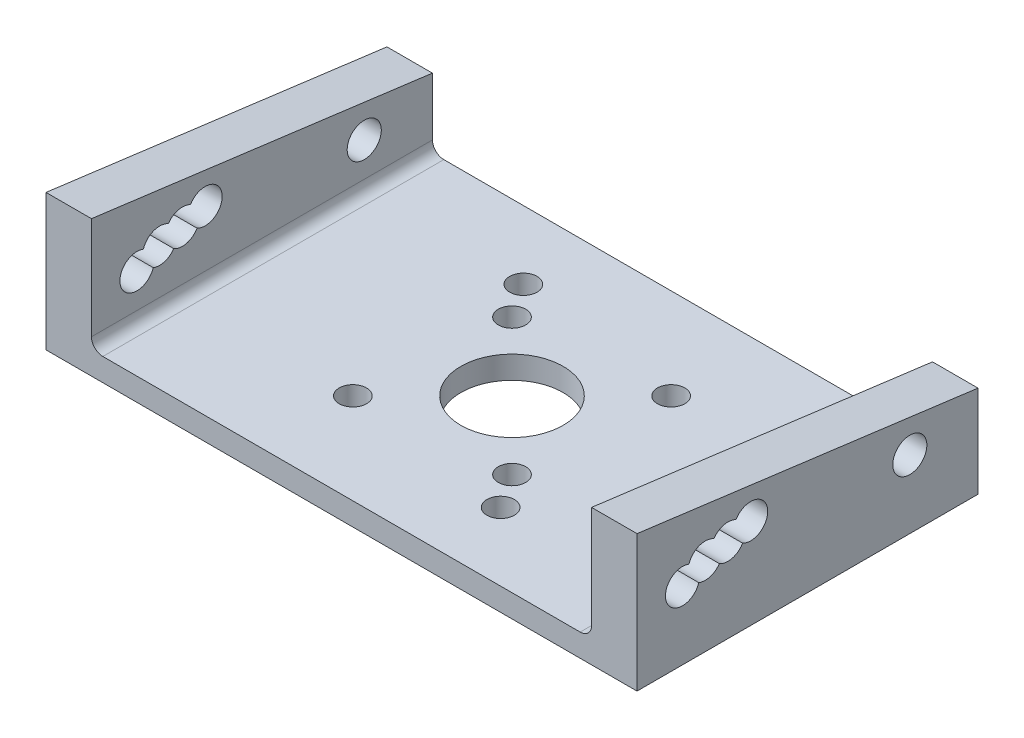
SolidWorks part; units mm, degrees
material "Náilon 6/10"
ref_plane "Plano frontal" through (0, 0, 0) normal (0, 0, 1) x (1, 0, 0)
ref_plane "Plano superior" through (0, 0, 0) normal (0, 1, 0) x (1, 0, 0)
ref_plane "Plano direito" through (0, 0, 0) normal (1, 0, 0) x (0, 0, -1)
sketch "Esboço1" plane through (0, 0, 0) normal (0, 1, 0) x (1, 0, 0)
  line L0 (0, 15) -> (0, -15) construction
  line L1 (-26, -15) -> (26, -15)
  line L2 (-26, -15) -> (-26, 15)
  line L3 (-26, 15) -> (26, 15)
  line L4 (26, -15) -> (26, 15)
  line L5 (0, -15) -> (43.0008, 30.964) construction
  circle A0 centre (0, 0) radius 4.5
  circle A1 centre (7, 7) radius 1.2058
  circle A2 centre (-6, 6) radius 1.2058
  circle A3 centre (-8, 9) radius 1.2058
  circle A4 centre (-7, -7) radius 1.2058
  circle A5 centre (6, -6) radius 1.2058
  circle A6 centre (8, -9) radius 1.2058
  point P5 (0, 15)
  dimension "D3" = 9
  dimension "D1" = 52
  dimension "D2" = 30
  dimension "D4" = 7
  dimension "D5" = 7
  dimension "D6" = 6
  dimension "D7" = 6
  dimension "D8" = 8
  dimension "D9" = 9
  dimension "D10" = 7
  dimension "D11" = 7
  dimension "D12" = 6
  dimension "D13" = 6
  dimension "D14" = 9
  dimension "D15" = 8
extrude "Ressalto-extrusão1" add sketch "Esboço1" along normal blind 2
sketch "Esboço2" plane through (-26, 0, 0) normal (-1, 0, 0) x (0, 0, 1)
  line L0 (-9, 6) -> (9, 6) construction
  line L1 (15, 12) -> (15, 2)
  line L2 (-9, 6) -> (5, 7.95) construction
  line L3 (-15, 2) -> (-15, 8.0894)
  line L5 (-15, 2) -> (15, 2) construction
  line L6 (-15, 8.0894) -> (15, 12)
  circle A0 centre (-9, 6) radius 1.5
  circle A1 centre (9, 6.94) radius 1.5
  circle A2 centre (7, 7.39) radius 1.5
  circle A3 centre (5, 7.95) radius 1.5
  circle A4 centre (11, 6) radius 1.5
  dimension "D1" = 18
  dimension "D3" = 3
  dimension "D5" = 1.39
  dimension "D9" = 3
  dimension "D2" = 6
  dimension "D4" = 0.94
  dimension "D6" = 16
  dimension "D7" = 14
  dimension "D8" = 1.95
  dimension "D10" = 4
  dimension "D11" = 20
  dimension "D12" = 10
extrude "Ressalto-extrusão2" add sketch "Esboço2" against normal blind 4
mirror "Espelhar1" about plane through (0, 0, 0) normal (1, 0, 0) of "Ressalto-extrusão2"
fillet "Filete3" radius 1 2 edges at (22, 2, 0)
